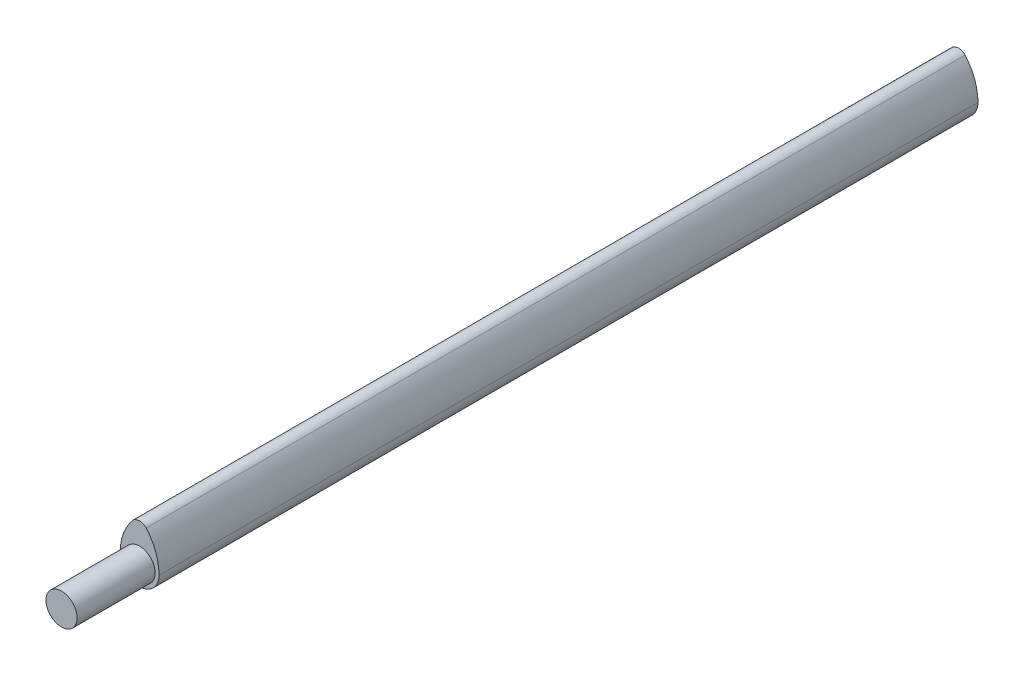
SolidWorks part; units mm, degrees
ref_plane "Front" through (0, 0, 0) normal (0, 0, 1) x (1, 0, 0)
ref_plane "Top" through (0, 0, 0) normal (0, 1, 0) x (1, 0, 0)
ref_plane "Right" through (0, 0, 0) normal (1, 0, 0) x (0, 0, -1)
sketch "Sketch1" plane through (0, 0, 0) normal (0, 0, 1) x (1, 0, 0)
  circle A0 centre (0, 0) radius 5
  dimension "D1" = 5
extrude "Boss-Extrude1" add sketch "Sketch1" against normal blind 210
sketch "Sketch2" plane through (0, 0, 0) normal (0, 0, 1) x (1, 0, 0)
  line L0 (-5, 0) -> (5, 0)
  circle A0 centre (0, 0) radius 5 construction
  arc A1 (-5, 0) -> (-1.7058, 8.8781) centre (8.6105, 0) cw
  arc A2 (5, 0) -> (1.7058, 8.8781) centre (-8.6105, 0) ccw
  arc A3 (-1.7058, 8.8781) -> (1.7058, 8.8781) centre (0, 7.1723) cw
  dimension "D3" = 13.6105
  dimension "D4" = 2.4124
  dimension "D1" = 10
extrude "Boss-Extrude2" add sketch "Sketch2" against normal blind 210
sketch "Sketch3" plane through (0, 0, 0) normal (0, 0, 1) x (1, 0, 0)
  circle A0 centre (0, 0) radius 3.9963
  dimension "D1" = 3.9963
extrude "Boss-Extrude3" add sketch "Sketch3" along normal blind 20
